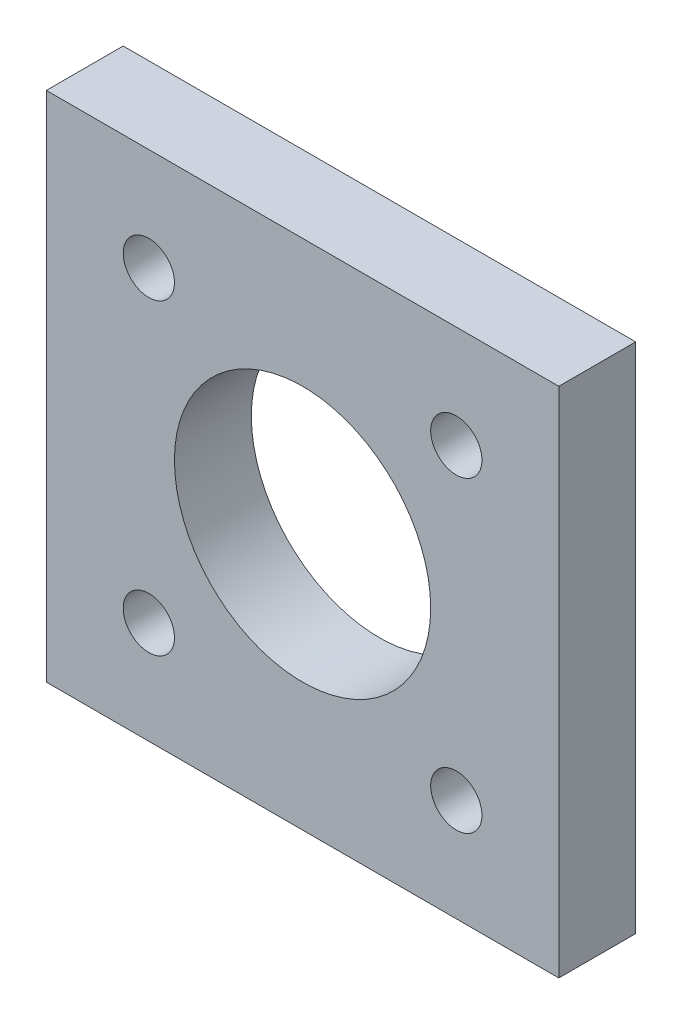
SolidWorks part; units mm, degrees
material "AISI 316 Annealed Stainless Steel Bar (SS)"
ref_plane "Front Plane" through (0, 0, 0) normal (0, 0, 1) x (1, 0, 0)
ref_plane "Top Plane" through (0, 0, 0) normal (0, 1, 0) x (1, 0, 0)
ref_plane "Right Plane" through (0, 0, 0) normal (1, 0, 0) x (0, 0, -1)
sketch "Sketch1" plane through (0, 0, 0) normal (0, 0, 1) x (1, 0, 0)
  line L1 (-20, -20) -> (20, -20)
  line L2 (-20, -20) -> (-20, 20)
  line L3 (-20, 20) -> (20, 20)
  line L4 (20, -20) -> (20, 20)
  line L5 (-20, -20) -> (20, 20) construction
  line L6 (-20, 20) -> (20, -20) construction
  circle A0 centre (0, 0) radius 10
  circle A1 centre (-12, 12) radius 2
  circle A2 centre (12, 12) radius 2
  circle A3 centre (12, -12) radius 2
  circle A4 centre (-12, -12) radius 2
  point P0 (0, 0)
  point P19 (0, 0)
  dimension "D1" = 20
  dimension "D2" = 4
  dimension "D5" = 8
  dimension "D6" = 4
  dimension "D3" = 40
  dimension "D4" = 40
extrude "Boss-Extrude1" add sketch "Sketch1" along normal blind 6
